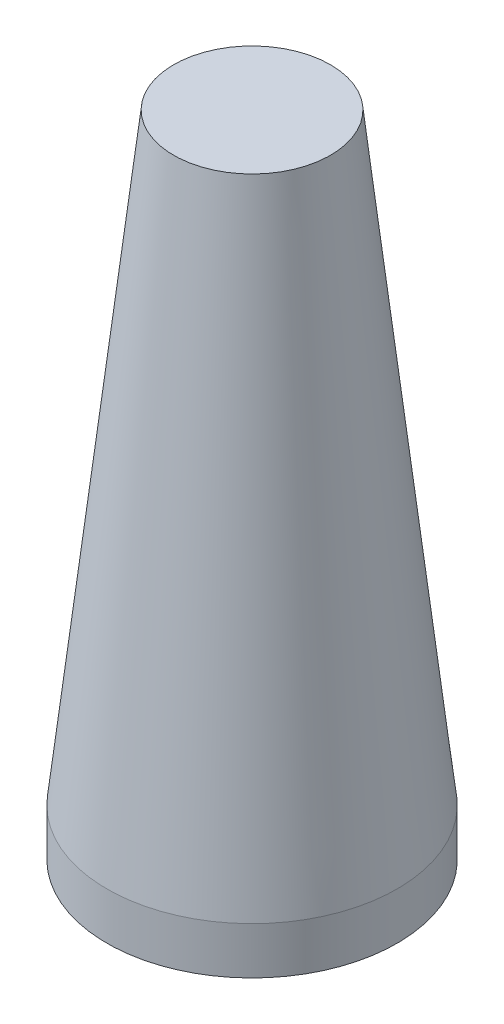
SolidWorks part; units mm, degrees
ref_plane "Front Plane" through (0, 0, 0) normal (0, 0, 1) x (1, 0, 0)
ref_plane "Top Plane" through (0, 0, 0) normal (0, 1, 0) x (1, 0, 0)
ref_plane "Right Plane" through (0, 0, 0) normal (1, 0, 0) x (0, 0, -1)
sketch "Sketch1" plane through (0, 0, 0) normal (0, 0, 1) x (1, 0, 0)
  line L0 (0, -27.499) -> (0, 800) construction
  line L1 (-178, 32.501) -> (-178, -27.499)
  line L2 (-20, 570) -> (-118.4295, 570)
  line L3 (0, 800) -> (-100, 800)
  line L4 (-185, -27.499) -> (-185, 32.501)
  line L5 (0, 790) -> (-94.0647, 790)
  line L6 (-27, 560) -> (-119.537, 560)
  line L7 (-178, -27.499) -> (-185, -27.499)
  line L8 (-100, 800) -> (-185, 32.501)
  line L9 (-94.0647, 790) -> (-118.4295, 570)
  line L10 (-119.537, 560) -> (-170.2419, 102.501)
  line L11 (-20, 92.501) -> (-171.3502, 92.501)
  line L12 (-27, 102.501) -> (-170.2419, 102.501)
  line L13 (-171.3502, 92.501) -> (-178, 32.501)
  line L14 (-20, 570) -> (-20, 92.501)
  line L15 (-27, 560) -> (-27, 102.501)
  dimension "D5" = 60
  dimension "D6" = 10
  dimension "D1" = 27.499
  dimension "D2" = 800
  dimension "D3" = 100
  dimension "D4" = 185
  dimension "D8" = 7
  dimension "D7" = 60
  dimension "D9" = 7
  dimension "D10" = 220
  dimension "D11" = 20
  dimension "D12" = 20
  dimension "D13" = 60
  dimension "D14" = 27
  dimension "D15" = 10
  dimension "D16" = 7
  dimension "D17" = 7
  dimension "D18" = 10
revolve "Revolve1" add sketch "Sketch1" angle 360 about L0
